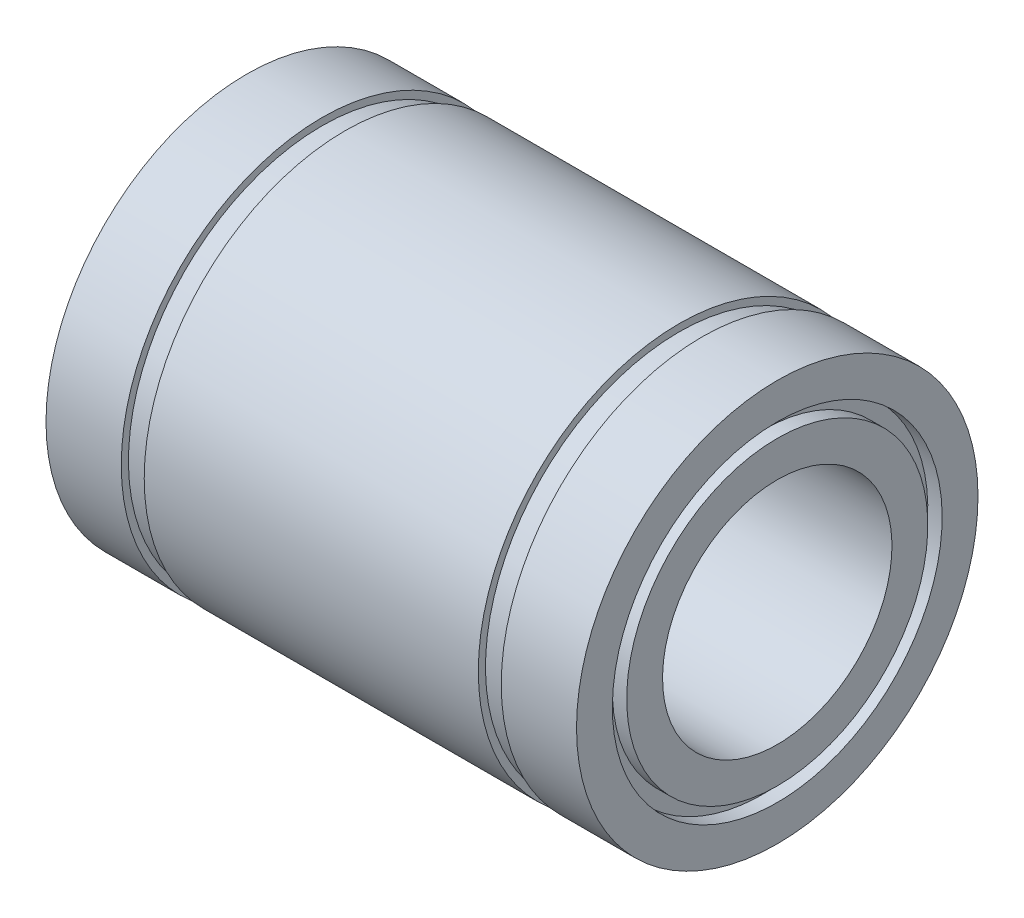
SolidWorks part; units mm, degrees
material "Ст3сп ГОСТ 535-2005"
ref_plane "Plano frontal" through (0, 0, 0) normal (0, 0, 1) x (1, 0, 0)
ref_plane "Plano superior" through (0, 0, 0) normal (0, 1, 0) x (1, 0, 0)
ref_plane "Plano direito" through (0, 0, 0) normal (1, 0, 0) x (0, 0, -1)
sketch "Esboço1" plane through (0, 0, 0) normal (0, 0, 1) x (1, 0, 0)
  line L0 (-18.5, 14) -> (-13.25, 14)
  line L1 (-13.25, 14) -> (-13.25, 13.5)
  line L2 (-13.25, 13.5) -> (-11.65, 13.5)
  line L3 (-11.65, 13.5) -> (-11.65, 14)
  line L4 (-11.65, 14) -> (11.65, 14)
  line L5 (11.65, 14) -> (11.65, 13.5)
  line L6 (11.65, 13.5) -> (13.25, 13.5)
  line L7 (13.25, 13.5) -> (13.25, 14)
  line L8 (13.25, 14) -> (18.5, 14)
  line L9 (18.5, 14) -> (18.5, 11.5)
  line L10 (18.5, 8) -> (-18.5, 8)
  line L11 (-18.5, 8) -> (-18.5, 10.5)
  line L12 (0, 8) -> (0, 0) construction
  line L13 (0, 0) -> (-86.5, 0) construction
  line L14 (-18.5, 11.5) -> (-18.5, 14)
  line L15 (-18.5, 11.5) -> (-17.5, 11.5)
  line L16 (18.5, 10.5) -> (18.5, 8)
  line L17 (-17.5, 11.5) -> (-17.5, 10.5)
  line L18 (-17.5, 10.5) -> (-18.5, 10.5)
  line L19 (18.5, 11.5) -> (17.5, 11.5)
  line L21 (18.5, 10.5) -> (17.5, 10.5)
  line L22 (17.5, 11.5) -> (17.5, 10.5)
  dimension "D1" = 37
  dimension "D2" = 26.5
  dimension "D3" = 1.6
  dimension "D4" = 16
  dimension "D5" = 28
  dimension "D6" = 27
  dimension "D7" = 1
  dimension "D8" = 1
  dimension "D9" = 1
  dimension "D10" = 1
revolve "Revolução1" add sketch "Esboço1" angle 360 about L13
